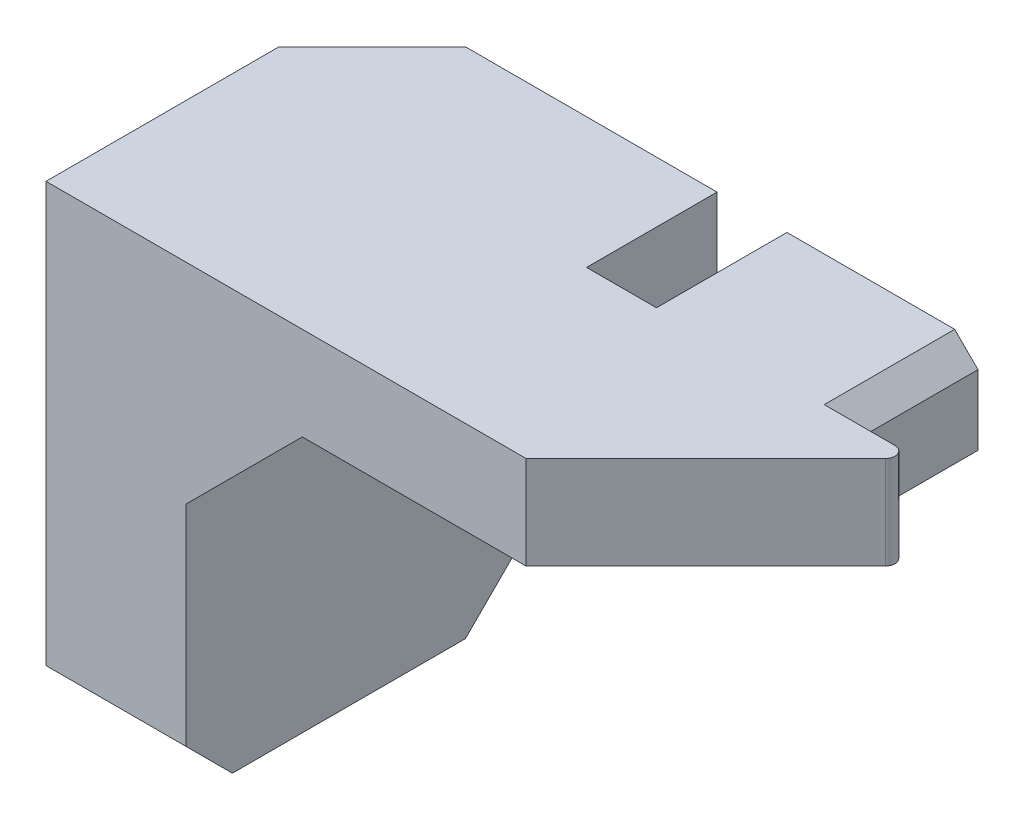
SolidWorks part; units mm, degrees
ref_plane "Front Plane" through (0, 0, 0) normal (0, 0, 1) x (1, 0, 0)
ref_plane "Top Plane" through (0, 0, 0) normal (0, 1, 0) x (1, 0, 0)
ref_plane "Right Plane" through (0, 0, 0) normal (1, 0, 0) x (0, 0, -1)
sketch "Sketch1" plane through (0, 0, 0) normal (0, 0, 1) x (1, 0, 0)
  line L0 (0, 0) -> (0, 25.4)
  line L1 (0, 25.4) -> (43.18, 25.4)
  line L2 (43.18, 25.4) -> (43.18, 20.32)
  line L3 (43.18, 20.32) -> (13.97, 20.32)
  line L4 (13.97, 20.32) -> (7.62, 13.97)
  line L5 (7.62, 13.97) -> (7.62, 0)
  line L6 (7.62, 0) -> (0, 0)
  dimension "D1" = 135
  dimension "D2" = 5.08
  dimension "D3" = 43.18
  dimension "D4" = 7.62
  dimension "D5" = 6.35
  dimension "D6" = 25.4
extrude "Boss-Extrude1" add sketch "Sketch1" along normal blind 17.78
sketch "Sketch4" plane through (0, 20.32, 0) normal (0, -1, 0) x (1, 0, 0)
  line L0 (13.97, 0) -> (43.18, 0) construction
  line L1 (21.336, 0) -> (18.796, 0)
  line L2 (21.336, 0) -> (21.336, 7.112)
  line L3 (21.336, 7.112) -> (18.796, 7.112)
  line L4 (18.796, 0) -> (18.796, 7.112)
  line L6 (33.02, 0) -> (33.02, 7.112)
  line L9 (13.97, 17.78) -> (13.97, 0) construction
  line L10 (33.02, 7.112) -> (36.83, 7.112)
  line L11 (36.83, 7.112) -> (26.162, 17.78)
  line L12 (13.97, 17.78) -> (43.18, 17.78) construction
  line L13 (26.162, 17.78) -> (43.18, 17.78)
  line L14 (43.18, 17.78) -> (43.18, 0)
  line L15 (43.18, 17.78) -> (43.18, 0) construction
  line L16 (43.18, 0) -> (33.02, 0)
  dimension "D1" = 7.112
  dimension "D2" = 7.366
  dimension "D3" = 19.05
  dimension "D4" = 2.54
  dimension "D5" = 45
  dimension "D6" = 3.81
extrude "Cut-Extrude2" cut sketch "Sketch4" against normal through all
sketch "Sketch3" plane through (0, 25.4, 0) normal (0, 1, 0) x (1, 0, 0)
  line L0 (0, 0) -> (0, -5.08)
  line L1 (0, -17.78) -> (0, 0) construction
  line L2 (0, -5.08) -> (5.08, 0)
  line L3 (18.796, 0) -> (0, 0) construction
  line L4 (5.08, 0) -> (0, 0)
  dimension "D1" = 5.08
extrude "Cut-Extrude1" cut sketch "Sketch3" against normal blind 5.08
chamfer "Chamfer3" distance 2.54 angle 45 2 edges at (3.81, 0, 0) (3.81, 0, 17.78)
fillet "Fillet2" radius 0.508 1 edges at (36.83, 22.86, 7.112)
chamfer "Chamfer4" distance 1.27 angle 45 2 edges at (33.02, 25.4, 3.556) (21.336, 25.4, 3.556)
